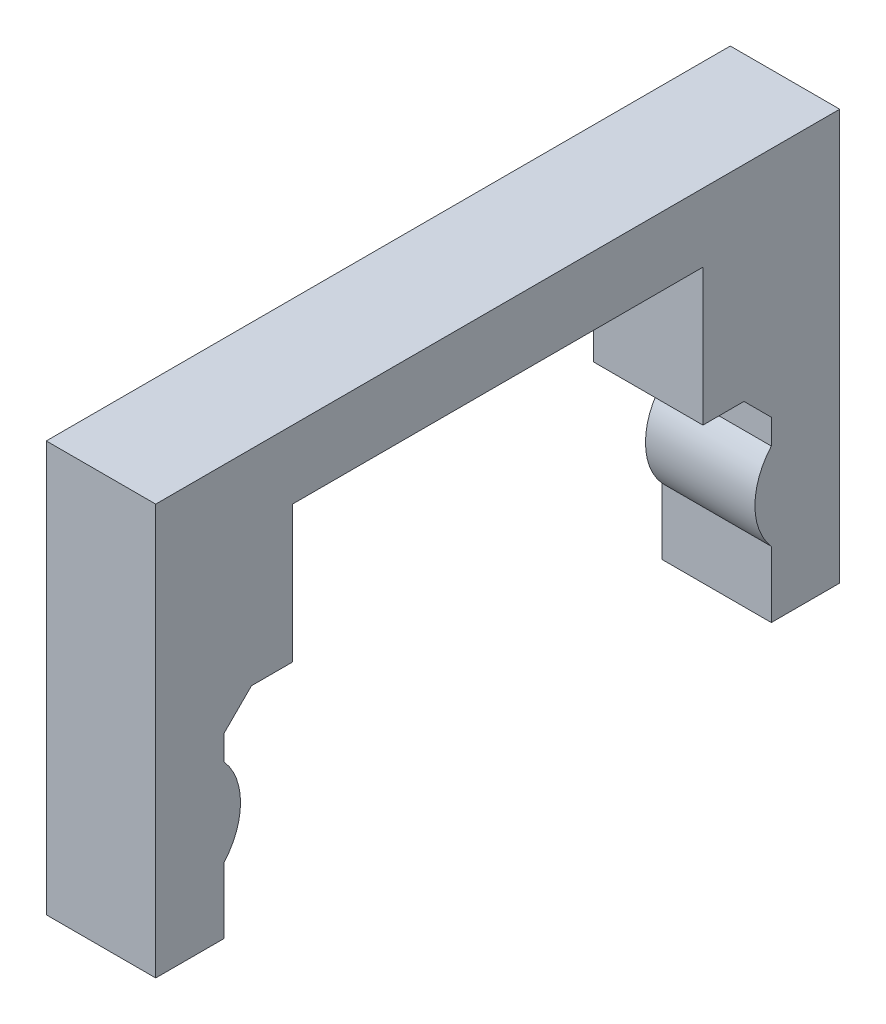
SolidWorks part; units mm, degrees
ref_plane "Front Plane" through (0, 0, 0) normal (0, 0, 1) x (1, 0, 0)
ref_plane "Top Plane" through (0, 0, 0) normal (0, 1, 0) x (1, 0, 0)
ref_plane "Right Plane" through (0, 0, 0) normal (1, 0, 0) x (0, 0, -1)
sketch "Sketch3" plane through (0, 0, 0) normal (1, 0, 0) x (0, 0, -1)
  line L0 (-101.8456, -9.1027) -> (-95.4956, -9.1027)
  line L1 (-95.4956, -9.1027) -> (-95.4956, 9.9473)
  line L2 (-95.4956, 9.9473) -> (-89.1456, 9.9473)
  line L3 (-89.1456, 9.9473) -> (-89.1456, 22.6473)
  line L4 (-89.1456, 22.6473) -> (-51.0456, 22.6473)
  line L5 (-51.0456, 22.6473) -> (-51.0456, 9.9473)
  line L6 (-51.0456, 9.9473) -> (-44.6956, 9.9473)
  line L7 (-44.6956, 9.9473) -> (-44.6956, -9.1027)
  line L8 (-44.6956, -9.1027) -> (-38.3456, -9.1027)
  line L9 (-38.3456, -9.1027) -> (-38.3456, 28.9973)
  line L10 (-38.3456, 28.9973) -> (-101.8456, 28.9973)
  line L11 (-101.8456, 28.9973) -> (-101.8456, -9.1027)
  dimension "D1" = 6.35
  dimension "D2" = 6.35
  dimension "D3" = 6.35
  dimension "D4" = 6.35
  dimension "D5" = 12.7
  dimension "D6" = 6.35
  dimension "D7" = 50.8
  dimension "D8" = 12.7
  dimension "D9" = 38.1
  dimension "D10" = 38.1
extrude "Boss-Extrude1" add sketch "Sketch3" along normal blind 10.16
sketch "Sketch4" plane through (10.16, 0, 0) normal (1, 0, 0) x (0, 0, -1)
  line L0 (-95.4956, 9.9473) -> (-89.1456, 9.9473) construction
  line L1 (-51.0456, 9.9473) -> (-44.6956, 9.9473) construction
  line L2 (-95.4956, -9.1027) -> (-95.4956, 9.9473) construction
  line L3 (-44.6956, 9.9473) -> (-44.6956, -9.1027) construction
  line L4 (-101.8456, -4.7736) -> (-101.8456, 6.8883)
  line L5 (-101.8456, 28.9973) -> (-101.8456, -9.1027) construction
  line L6 (-38.3456, -4.7736) -> (-38.3456, 6.8883)
  line L7 (-38.3456, -9.1027) -> (-38.3456, 28.9973) construction
  arc A0 (-101.8456, -4.7736) -> (-101.8456, 6.8883) centre (-100.0676, 1.0573) ccw
  arc A1 (-38.3456, 6.8883) -> (-38.3456, -4.7736) centre (-40.1236, 1.0573) ccw
  point P4 (-92.3206, 9.9473)
  dimension "D3" = 12.192
  dimension "D4" = 12.192
  dimension "D1" = 8.89
  dimension "D2" = 8.89
  dimension "D5" = 4.572
  dimension "D6" = 4.572
extrude "Boss-Extrude2" add sketch "Sketch4" against normal blind 10.16
chamfer "Chamfer1" distance 2.54 angle 45 2 edges at (5.08, 9.9473, 95.4956) (5.08, 9.9473, 44.6956)
